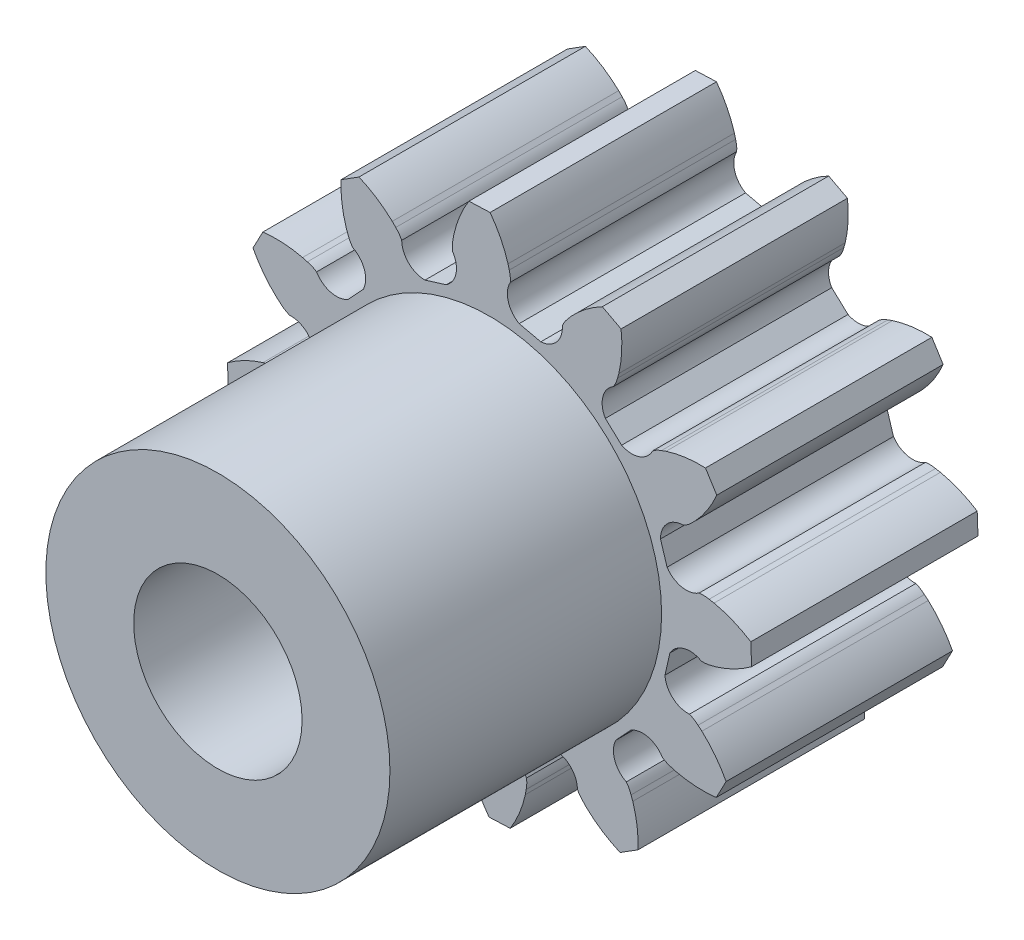
SolidWorks part; units mm, degrees
ref_plane "Front Plane" through (0, 0, 0) normal (0, 0, 1) x (1, 0, 0)
ref_plane "Top Plane" through (0, 0, 0) normal (0, 1, 0) x (1, 0, 0)
ref_plane "Right Plane" through (0, 0, 0) normal (1, 0, 0) x (0, 0, -1)
sketch "Model" plane through (0, 0, 0) normal (0, 0, 1) x (1, 0, 0)
  line L0 (60.3405, 63.9983) -> (60.4299, 64.1061)
  line L1 (61.3137, 64.786) -> (61.8393, 64.5089)
  line L2 (61.7774, 63.3955) -> (61.7391, 63.2608)
  line L3 (61.3986, 62.1158) -> (61.8553, 61.6928)
  line L4 (62.9709, 62.12) -> (63.1022, 62.1686)
  line L5 (64.2076, 62.3155) -> (64.5242, 61.8127)
  line L6 (63.914, 60.8794) -> (63.8134, 60.782)
  line L7 (62.946, 59.9606) -> (63.13, 59.3659)
  line L8 (64.3098, 59.1781) -> (64.4478, 59.1545)
  line L9 (65.4786, 58.729) -> (65.5013, 58.1354)
  line L10 (64.5062, 57.6322) -> (64.3704, 57.5981)
  line L11 (63.2085, 57.3205) -> (63.0705, 56.7134)
  line L12 (63.9983, 55.9609) -> (64.1061, 55.8714)
  line L13 (64.786, 54.9876) -> (64.5089, 54.4621)
  line L14 (63.3955, 54.5239) -> (63.2608, 54.5623)
  line L15 (62.1158, 54.9028) -> (61.6928, 54.446)
  line L16 (62.12, 53.3304) -> (62.1686, 53.1991)
  line L17 (62.3155, 52.0937) -> (61.8127, 51.7771)
  line L18 (60.8794, 52.3874) -> (60.782, 52.488)
  line L19 (59.9606, 53.3554) -> (59.3659, 53.1713)
  line L20 (59.1781, 51.9916) -> (59.1545, 51.8535)
  line L21 (58.729, 50.8228) -> (58.1354, 50.8)
  line L22 (57.6322, 51.7951) -> (57.5981, 51.931)
  line L23 (57.3205, 53.0928) -> (56.7134, 53.2308)
  line L24 (55.9609, 52.303) -> (55.8714, 52.1953)
  line L25 (54.9876, 51.5153) -> (54.4621, 51.7925)
  line L26 (54.5239, 52.9059) -> (54.5623, 53.0405)
  line L27 (54.9028, 54.1856) -> (54.446, 54.6086)
  line L28 (53.3304, 54.1814) -> (53.1991, 54.1328)
  line L29 (52.0937, 53.9858) -> (51.7771, 54.4886)
  line L30 (52.3874, 55.4219) -> (52.488, 55.5193)
  line L31 (53.3554, 56.3407) -> (53.1713, 56.9355)
  line L32 (51.9916, 57.1233) -> (51.8535, 57.1469)
  line L33 (50.8228, 57.5723) -> (50.8, 58.166)
  line L34 (51.7951, 58.6691) -> (51.931, 58.7032)
  line L35 (53.0928, 58.9809) -> (53.2308, 59.588)
  line L36 (52.303, 60.3405) -> (52.1953, 60.4299)
  line L37 (51.5153, 61.3137) -> (51.7925, 61.8393)
  line L38 (52.9059, 61.7774) -> (53.0405, 61.7391)
  line L39 (54.1856, 61.3986) -> (54.6086, 61.8553)
  line L40 (54.1814, 62.9709) -> (54.1328, 63.1022)
  line L41 (53.9858, 64.2076) -> (54.4886, 64.5242)
  line L42 (55.4219, 63.914) -> (55.5193, 63.8134)
  line L43 (56.3407, 62.946) -> (56.9355, 63.13)
  line L44 (57.1233, 64.3098) -> (57.1469, 64.4478)
  line L45 (57.5723, 65.4786) -> (58.166, 65.5013)
  line L46 (58.6691, 64.5062) -> (58.7032, 64.3704)
  line L47 (58.9809, 63.2085) -> (59.588, 63.0705)
  circle A0 centre (58.1507, 58.1507) radius 2.3622
  arc A1 (59.588, 63.0705) -> (60.1915, 63.7579) centre (59.5461, 63.716) ccw
  arc A2 (60.3405, 63.9983) -> (60.1915, 63.7579) centre (60.9084, 63.4801) ccw
  arc A3 (61.3137, 64.786) -> (60.4299, 64.1061) centre (62.8118, 61.9243) ccw
  arc A4 (61.7774, 63.3955) -> (61.8393, 64.5089) centre (58.6317, 64.1286) ccw
  arc A5 (61.6248, 63.0021) -> (61.7391, 63.2608) centre (60.9907, 63.4367) ccw
  arc A6 (61.6248, 63.0021) -> (61.3986, 62.1158) centre (61.9548, 62.4458) ccw
  arc A7 (61.8553, 61.6928) -> (62.7217, 61.9862) centre (62.1418, 62.2727) ccw
  arc A8 (62.9709, 62.12) -> (62.7217, 61.9862) centre (63.2036, 61.3873) ccw
  arc A9 (64.2076, 62.3155) -> (63.1022, 62.1686) centre (64.0742, 59.0882) ccw
  arc A10 (63.914, 60.8794) -> (64.5242, 61.8127) centre (61.5562, 63.0872) ccw
  arc A11 (63.585, 60.6151) -> (63.8134, 60.782) centre (63.2532, 61.3085) ccw
  arc A12 (63.585, 60.6151) -> (62.946, 59.9606) centre (63.5927, 59.9683) ccw
  arc A13 (63.13, 59.3659) -> (64.0271, 59.1868) centre (63.6681, 59.7249) ccw
  arc A14 (64.3098, 59.1781) -> (64.0271, 59.1868) centre (64.145, 58.4272) ccw
  arc A15 (65.4786, 58.729) -> (64.4478, 59.1545) centre (63.7493, 56.0008) ccw
  arc A16 (64.5062, 57.6322) -> (65.5013, 58.1354) centre (63.5682, 60.7231) ccw
  arc A17 (64.0892, 57.5677) -> (64.3704, 57.5981) centre (64.1485, 58.3342) ccw
  arc A18 (64.0892, 57.5677) -> (63.2085, 57.3205) centre (63.7724, 57.0037) ccw
  arc A19 (63.0705, 56.7134) -> (63.7579, 56.1098) centre (63.716, 56.7553) ccw
  arc A20 (63.9983, 55.9609) -> (63.7579, 56.1098) centre (63.4801, 55.393) ccw
  arc A21 (64.786, 54.9876) -> (64.1061, 55.8714) centre (61.9243, 53.4895) ccw
  arc A22 (63.3955, 54.5239) -> (64.5089, 54.4621) centre (64.1286, 57.6697) ccw
  arc A23 (63.0021, 54.6766) -> (63.2608, 54.5623) centre (63.4367, 55.3107) ccw
  arc A24 (63.0021, 54.6766) -> (62.1158, 54.9028) centre (62.4458, 54.3465) ccw
  arc A25 (61.6928, 54.446) -> (61.9862, 53.5796) centre (62.2727, 54.1596) ccw
  arc A26 (62.12, 53.3304) -> (61.9862, 53.5796) centre (61.3873, 53.0977) ccw
  arc A27 (62.3155, 52.0937) -> (62.1686, 53.1991) centre (59.0882, 52.2272) ccw
  arc A28 (60.8794, 52.3874) -> (61.8127, 51.7771) centre (63.0872, 54.7452) ccw
  arc A29 (60.6151, 52.7163) -> (60.782, 52.488) centre (61.3085, 53.0481) ccw
  arc A30 (60.6151, 52.7163) -> (59.9606, 53.3554) centre (59.9683, 52.7086) ccw
  arc A31 (59.3659, 53.1713) -> (59.1868, 52.2743) centre (59.7249, 52.6333) ccw
  arc A32 (59.1781, 51.9916) -> (59.1868, 52.2743) centre (58.4272, 52.1564) ccw
  arc A33 (58.729, 50.8228) -> (59.1545, 51.8535) centre (56.0008, 52.552) ccw
  arc A34 (57.6322, 51.7951) -> (58.1354, 50.8) centre (60.7231, 52.7332) ccw
  arc A35 (57.5677, 52.2122) -> (57.5981, 51.931) centre (58.3342, 52.1528) ccw
  arc A36 (57.5677, 52.2122) -> (57.3205, 53.0928) centre (57.0037, 52.5289) ccw
  arc A37 (56.7134, 53.2308) -> (56.1098, 52.5435) centre (56.7553, 52.5854) ccw
  arc A38 (55.9609, 52.303) -> (56.1098, 52.5435) centre (55.393, 52.8212) ccw
  arc A39 (54.9876, 51.5153) -> (55.8714, 52.1953) centre (53.4895, 54.377) ccw
  arc A40 (54.5239, 52.9059) -> (54.4621, 51.7925) centre (57.6697, 52.1728) ccw
  arc A41 (54.6766, 53.2993) -> (54.5623, 53.0405) centre (55.3107, 52.8646) ccw
  arc A42 (54.6766, 53.2993) -> (54.9028, 54.1856) centre (54.3465, 53.8555) ccw
  arc A43 (54.446, 54.6086) -> (53.5796, 54.3151) centre (54.1596, 54.0287) ccw
  arc A44 (53.3304, 54.1814) -> (53.5796, 54.3151) centre (53.0977, 54.9141) ccw
  arc A45 (52.0937, 53.9858) -> (53.1991, 54.1328) centre (52.2272, 57.2132) ccw
  arc A46 (52.3874, 55.4219) -> (51.7771, 54.4886) centre (54.7452, 53.2142) ccw
  arc A47 (52.7163, 55.6863) -> (52.488, 55.5193) centre (53.0481, 54.9928) ccw
  arc A48 (52.7163, 55.6863) -> (53.3554, 56.3407) centre (52.7086, 56.333) ccw
  arc A49 (53.1713, 56.9355) -> (52.2743, 57.1145) centre (52.6333, 56.5765) ccw
  arc A50 (51.9916, 57.1233) -> (52.2743, 57.1145) centre (52.1564, 57.8742) ccw
  arc A51 (50.8228, 57.5723) -> (51.8535, 57.1469) centre (52.552, 60.3005) ccw
  arc A52 (51.7951, 58.6691) -> (50.8, 58.166) centre (52.7332, 55.5783) ccw
  arc A53 (52.2122, 58.7336) -> (51.931, 58.7032) centre (52.1528, 57.9672) ccw
  arc A54 (52.2122, 58.7336) -> (53.0928, 58.9809) centre (52.5289, 59.2976) ccw
  arc A55 (53.2308, 59.588) -> (52.5435, 60.1915) centre (52.5854, 59.5461) ccw
  arc A56 (52.303, 60.3405) -> (52.5435, 60.1915) centre (52.8212, 60.9084) ccw
  arc A57 (51.5153, 61.3137) -> (52.1953, 60.4299) centre (54.377, 62.8118) ccw
  arc A58 (52.9059, 61.7774) -> (51.7925, 61.8393) centre (52.1728, 58.6317) ccw
  arc A59 (53.2993, 61.6248) -> (53.0405, 61.7391) centre (52.8646, 60.9907) ccw
  arc A60 (53.2993, 61.6248) -> (54.1856, 61.3986) centre (53.8555, 61.9548) ccw
  arc A61 (54.6086, 61.8553) -> (54.3151, 62.7217) centre (54.0287, 62.1418) ccw
  arc A62 (54.1814, 62.9709) -> (54.3151, 62.7217) centre (54.9141, 63.2036) ccw
  arc A63 (53.9858, 64.2076) -> (54.1328, 63.1022) centre (57.2132, 64.0742) ccw
  arc A64 (55.4219, 63.914) -> (54.4886, 64.5242) centre (53.2142, 61.5562) ccw
  arc A65 (55.6863, 63.585) -> (55.5193, 63.8134) centre (54.9928, 63.2532) ccw
  arc A66 (55.6863, 63.585) -> (56.3407, 62.946) centre (56.333, 63.5927) ccw
  arc A67 (56.9355, 63.13) -> (57.1145, 64.0271) centre (56.5765, 63.6681) ccw
  arc A68 (57.1233, 64.3098) -> (57.1145, 64.0271) centre (57.8742, 64.145) ccw
  arc A69 (57.5723, 65.4786) -> (57.1469, 64.4478) centre (60.3005, 63.7493) ccw
  arc A70 (58.6691, 64.5062) -> (58.166, 65.5013) centre (55.5783, 63.5682) ccw
  arc A71 (58.7336, 64.0892) -> (58.7032, 64.3704) centre (57.9672, 64.1485) ccw
  arc A72 (58.7336, 64.0892) -> (58.9809, 63.2085) centre (59.2976, 63.7724) ccw
extrude "Boss-Extrude1" add sketch "Model" along normal blind 6.35
sketch "Sketch2" plane through (0, 0, 6.35) normal (0, 0, 1) x (1, 0, 0)
  circle A0 centre (58.1507, 58.1507) radius 4.826
  circle A1 centre (58.1507, 58.1507) radius 2.3622
  dimension "D1" = 9.652
extrude "Boss-Extrude2" add sketch "Sketch2" along normal blind 7.62
